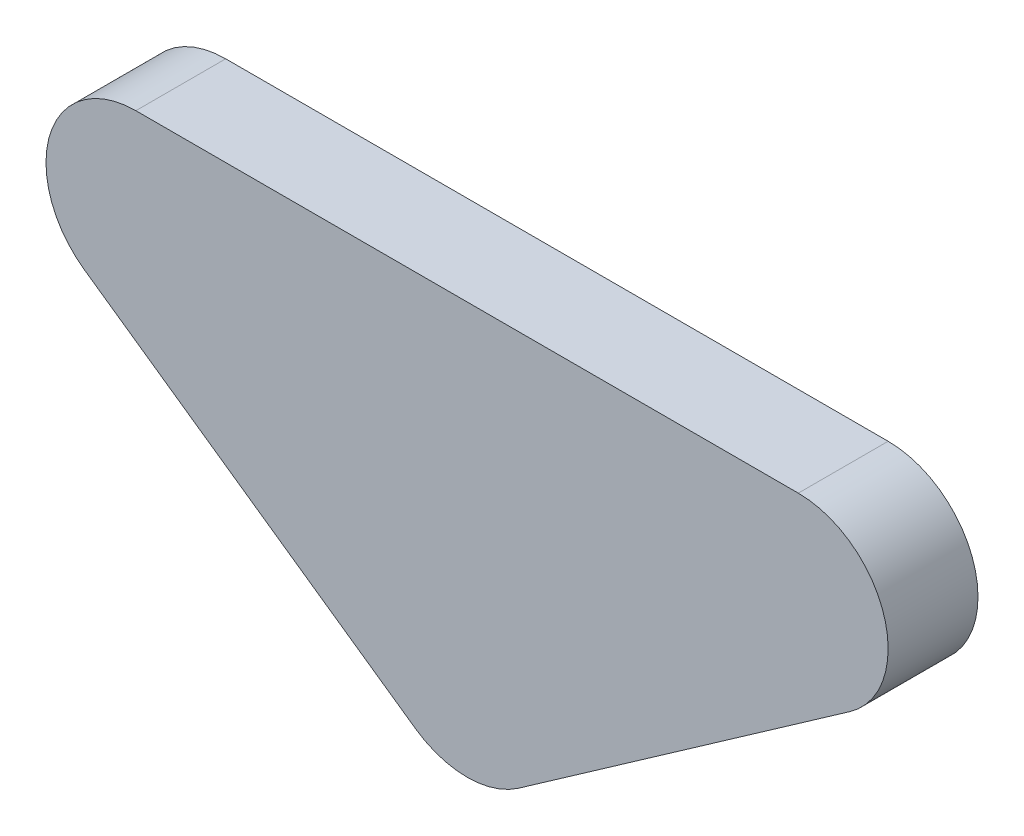
SolidWorks part; units mm, degrees
ref_plane "前视基准面" through (0, 0, 0) normal (0, 0, 1) x (1, 0, 0)
ref_plane "上视基准面" through (0, 0, 0) normal (0, 1, 0) x (1, 0, 0)
ref_plane "右视基准面" through (0, 0, 0) normal (1, 0, 0) x (0, 0, -1)
sketch "草图1" plane through (0, 0, 0) normal (0, 0, 1) x (1, 0, 0)
  line L0 (5.7358, -8.1915) -> (42.5976, 17.6194)
  line L1 (36.8618, 35.8109) -> (-36.8618, 35.8109)
  line L2 (-42.5976, 17.6194) -> (-5.7358, -8.1915)
  arc A0 (-5.7358, -8.1915) -> (5.7358, -8.1915) centre (0, 0) ccw
  arc A1 (36.8618, 35.8109) -> (42.5976, 17.6194) centre (36.8618, 25.8109) cw
  arc A2 (-36.8618, 35.8109) -> (-42.5976, 17.6194) centre (-36.8618, 25.8109) ccw
  dimension "D3" = 10
  dimension "D1" = 45
  dimension "D2" = 45
  dimension "D4" = 110
extrude "凸台-拉伸1" add sketch "草图1" along normal blind 10
